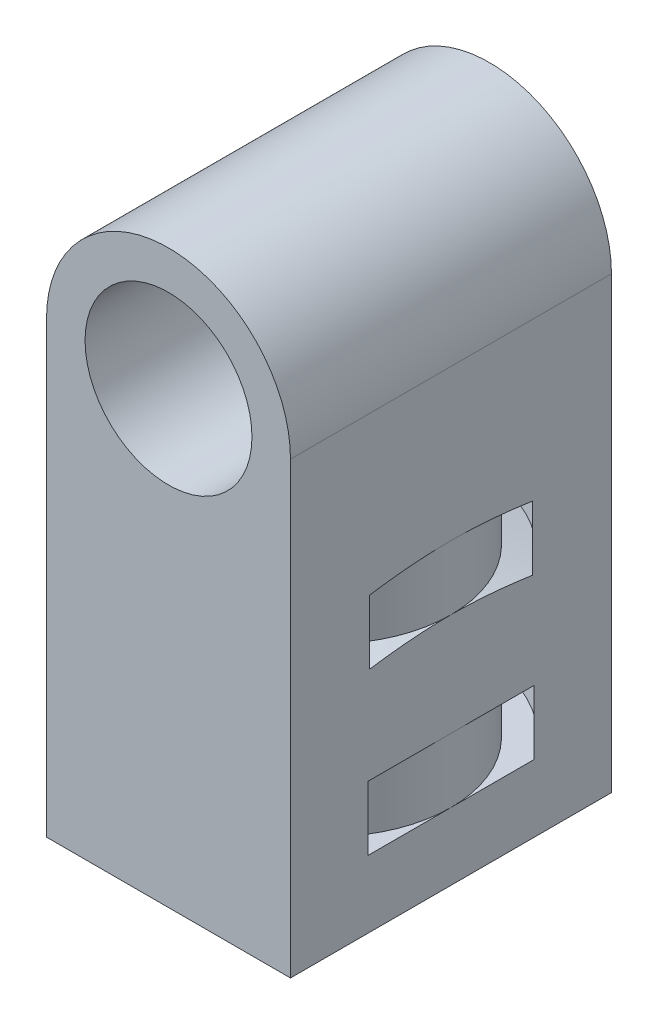
SolidWorks part; units mm, degrees
ref_plane "Alzado" through (0, 0, 0) normal (0, 0, 1) x (1, 0, 0)
ref_plane "Planta" through (0, 0, 0) normal (0, 1, 0) x (1, 0, 0)
ref_plane "Vista lateral" through (0, 0, 0) normal (1, 0, 0) x (0, 0, -1)
sketch "Croquis1" plane through (0, 0, 0) normal (0, 0, 1) x (1, 0, 0)
  line L0 (0, 0) -> (0, -10) construction
  line L1 (-9.5, -10) -> (9.5, -10)
  line L2 (-9.5, -10) -> (-9.5, 0)
  line L3 (9.5, -10) -> (9.5, 0)
  circle A0 centre (0, 0) radius 6.5
  arc A1 (9.5, 0) -> (-9.5, 0) centre (0, 0) ccw
  point P8 (0, -10)
  dimension "D1" = 13
  dimension "D2" = 3
  dimension "D3" = 10
extrude "Saliente-Extruir1" add sketch "Croquis1" against normal mid plane 25
ref_plane "Plano1" through (0, -10, 0) normal (0, -1, 0) x (-1, 0, 0)
sketch "Croquis3" plane through (0, -10, 0) normal (0, -1, 0) x (-1, 0, 0)
  line L0 (9.5, -12.5) -> (-9.5, -12.5) construction
  line L1 (9.5, 12.5) -> (9.5, -12.5) construction
  line L2 (-9.5, 12.5) -> (-9.5, -12.5) construction
  line L3 (9.5, 12.5) -> (-9.5, 12.5) construction
  line L4 (9.5, -12.5) -> (-9.5, -12.5)
  line L5 (9.5, 12.5) -> (9.5, -12.5)
  line L6 (-9.5, 12.5) -> (-9.5, -12.5)
  line L7 (9.5, 12.5) -> (-9.5, 12.5)
  circle A0 centre (0, 0) radius 6.5
  dimension "D1" = 13
extrude "Saliente-Extruir2" add sketch "Croquis3" along normal blind 25
sketch "Croquis8" plane through (0, 0, 0) normal (0, 0, 1) x (1, 0, 0)
  line L0 (0, -6.5) -> (0, -35) construction
  line L1 (9.5, -35) -> (-9.5, -35) construction
  line L2 (-9.5, 0) -> (-9.5, -35) construction
  line L3 (9.5, -35) -> (9.5, 0) construction
  line L4 (-9.5, -20.75) -> (9.5, -20.75) construction
  line L5 (-11.4346, -17.2573) -> (-11.4346, -12.2573)
  line L6 (-11.5, -24.75) -> (-9.5, -24.75)
  line L7 (-11.5, -24.75) -> (-11.5, -29.75)
  line L8 (-11.5, -29.75) -> (-9.5, -29.75)
  line L9 (-9.5, -24.75) -> (-9.5, -29.75)
  line L10 (-11.4346, -12.2573) -> (-9.5, -11.75)
  line L11 (-11.4346, -17.2573) -> (-9.5, -16.75)
  line L12 (-9.5, -16.75) -> (-9.5, -11.75)
  circle A0 centre (0, 0) radius 6.5 construction
  point P8 (0, -20.75)
  dimension "D1" = 28.5
  dimension "D2" = 2
  dimension "D3" = 5
  dimension "D4" = 4
  dimension "D5" = 2
  dimension "D6" = 5
revolve "Cortar-Revolución1" cut sketch "Croquis8" angle 360 about L0
